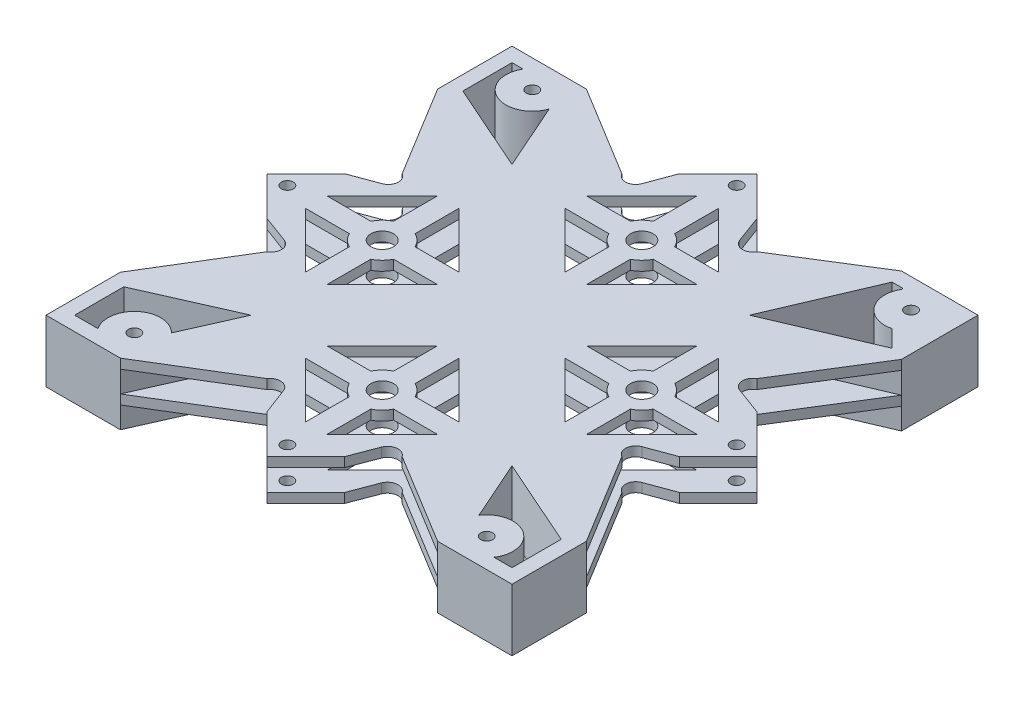
SolidWorks part; units mm, degrees
material "ABS"
ref_plane "Front Plane" through (0, 0, 0) normal (0, 0, 1) x (1, 0, 0)
ref_plane "Top Plane" through (0, 0, 0) normal (0, 1, 0) x (1, 0, 0)
ref_plane "Right Plane" through (0, 0, 0) normal (1, 0, 0) x (0, 0, -1)
sketch "Sketch1" plane through (0, 0, 0) normal (0, 1, 0) x (1, 0, 0)
  line L1 (0, 0) -> (97.6, 0)
  line L2 (0, 0) -> (0, 97.6)
  line L3 (0, 97.6) -> (97.6, 97.6)
  line L4 (97.6, 0) -> (97.6, 97.6)
  dimension "D1" = 97.6
  dimension "D2" = 97.6
extrude "Boss-Extrude1" add sketch "Sketch1" along normal blind 2
sketch "Sketch2" plane through (0, 0, 0) normal (0, -1, 0) x (-1, 0, 0)
  line L0 (-97.6, 97.6) -> (0, 0) construction
  line L1 (-97.6, 0) -> (0, 97.6) construction
  line L2 (-48.8, 97.6) -> (-48.8, 0) construction
  line L3 (-97.6, 97.6) -> (0, 97.6) construction
  line L4 (0, 0) -> (-97.6, 0) construction
  line L5 (-97.6, 48.8) -> (0, 48.8) construction
  line L6 (-97.6, 0) -> (-97.6, 97.6) construction
  line L7 (0, 97.6) -> (0, 0) construction
sketch "Sketch3" plane through (0, 0, 0) normal (0, -1, 0) x (1, 0, 0)
  line L0 (97.6, -97.6) -> (0, -97.6) construction
  line L1 (97.6, 0) -> (97.6, -97.6) construction
  line L2 (0, -97.6) -> (0, 0) construction
  line L3 (0, 0) -> (97.6, 0) construction
  line L4 (97.6, -94.6) -> (0, -94.6) construction
  line L5 (3, -97.6) -> (3, 0) construction
  line L6 (3, -94.6) -> (5.3161, -94.6)
  line L7 (3, -94.6) -> (3, -84.3)
  line L8 (3, -84.3) -> (21.4728, -76.1272)
  line L9 (97.6, 0) -> (0, -97.6) construction
  line L10 (21.4728, -76.1272) -> (13.3, -94.6)
  line L11 (21.4728, -21.4728) -> (13.3, -3)
  line L12 (3, -3) -> (13.3, -3)
  line L13 (0, -3) -> (97.6, -3) construction
  line L14 (3, -13.3) -> (3, -3)
  line L15 (3, -3) -> (7.8732, -3)
  line L16 (3, -13.3) -> (21.4728, -21.4728)
  line L17 (97.6, -97.6) -> (0, 0) construction
  line L18 (0, -97.6) -> (0, 0) construction
  line L19 (16.1614, -10.109) -> (21.4728, -21.4728) construction
  line L20 (94.6, -97.6) -> (94.6, 0) construction
  line L21 (94.6, -3) -> (94.6, -13.3)
  line L22 (94.6, -3) -> (84.3, -3)
  line L23 (94.6, -13.3) -> (76.1272, -21.4728)
  line L24 (76.1272, -21.4728) -> (84.3, -3)
  line L25 (94.6, -82.6) -> (73.6741, -73.6741)
  line L26 (73.6741, -73.6741) -> (82.6, -94.6)
  line L27 (94.6, -82.6) -> (82.6, -94.6) construction
  line L28 (94.6, -82.6) -> (91.0273, -86.1727)
  line L29 (82.6, -94.6) -> (85.1169, -94.6)
  line L30 (3, -94.6) -> (13.3, -94.6) construction
  circle A0 centre (89.66, -91.5) radius 1.25
  circle A1 centre (10.05, -91.8) radius 1.25
  circle A2 centre (12.45, -6.05) radius 1.25
  circle A3 centre (86.25, -6.05) radius 1.25
  circle A4 centre (89.66, -91.5) radius 5.5
  circle A5 centre (10.05, -91.8) radius 5.5
  circle A6 centre (12.45, -6.05) radius 5.5
  circle A7 centre (86.25, -6.05) radius 5.5
  dimension "D1" = 6.1
  dimension "D9" = 3
  dimension "D16" = 3
  dimension "D20" = 2.5
  dimension "D21" = 11
  dimension "D23" = 11
  dimension "D24" = 2.5
  dimension "D26" = 11
  dimension "D27" = 11
  dimension "D2" = 7.94
  dimension "D3" = 5.8
  dimension "D4" = 10.05
  dimension "D5" = 6.05
  dimension "D6" = 12.45
  dimension "D7" = 6.05
  dimension "D8" = 11.35
  dimension "D10" = 3
  dimension "D11" = 10.3
  dimension "D12" = 20.2
  dimension "D13" = 3
  dimension "D14" = 10.3
  dimension "D15" = 20.2
  dimension "D17" = 10.3
  dimension "D18" = 22.75
  dimension "D19" = 15
  dimension "D22" = 10.3
  dimension "D25" = 20.2
extrude "Cut-Extrude1" cut sketch "Sketch3" against normal blind 10
fillet "Fillet1" radius 0.2 1 edges at (85.1169, 1, -94.6)
sketch "Sketch5" plane through (0, 0, 0) normal (0, -1, 0) x (1, 0, 0)
  line L0 (78.0601, -69.3344) -> (24.4532, -15.7275) construction
  line L1 (15.9101, -24.6358) -> (67.2589, -75.9846) construction
  line L2 (97.6, -97.6) -> (0, 0) construction
  line L3 (25.594, -80.7317) -> (80.9701, -25.3556) construction
  line L4 (71.5743, -17.3) -> (16.8047, -72.0696) construction
  line L5 (97.6, 0) -> (0, -97.6) construction
  line L6 (51.05, -89.7671) -> (51.05, -80.6171)
  line L7 (46.55, -89.7671) -> (46.55, -80.6171)
  line L8 (48.8, -97.6) -> (48.8, 0) construction
  line L9 (51.05, -89.7671) -> (62.5825, -78.2346)
  line L10 (62.5825, -78.2346) -> (53.4325, -78.2346)
  line L11 (44.1675, -78.2346) -> (35.0175, -78.2346)
  line L12 (35.0175, -78.2346) -> (46.55, -89.7671)
  line L13 (48.8, -78.2346) -> (36.0473, -78.2346) construction
  line L14 (48.8, -73.7346) -> (36.0473, -73.7346) construction
  line L15 (44.1675, -73.7346) -> (35.0175, -73.7346)
  line L16 (46.55, -71.3521) -> (46.55, -62.2021)
  line L17 (53.4325, -73.7346) -> (62.5825, -73.7346)
  line L18 (51.05, -71.3521) -> (51.05, -62.2021)
  line L19 (62.5825, -73.7346) -> (51.05, -62.2021)
  line L20 (46.55, -62.2021) -> (35.0175, -73.7346)
  line L21 (48.8, -48.8) -> (-2.5605, -100.1605) construction
  line L22 (48.8, -48.8) -> (97.6, 0) construction
  line L23 (97.6, -97.6) -> (0, 0) construction
  line L24 (73.7346, -48.8) -> (73.7346, -36.0473) construction
  line L25 (78.2346, -48.8) -> (78.2346, -36.0473) construction
  line L26 (62.2021, -46.55) -> (73.7346, -35.0175)
  line L27 (73.7346, -62.5825) -> (62.2021, -51.05)
  line L28 (71.3521, -51.05) -> (62.2021, -51.05)
  line L29 (73.7346, -53.4325) -> (73.7346, -62.5825)
  line L30 (71.3521, -46.55) -> (62.2021, -46.55)
  line L31 (73.7346, -44.1675) -> (73.7346, -35.0175)
  line L32 (78.2346, -35.0175) -> (89.7671, -46.55)
  line L33 (78.2346, -44.1675) -> (78.2346, -35.0175)
  line L34 (78.2346, -62.5825) -> (78.2346, -53.4325)
  line L35 (89.7671, -51.05) -> (78.2346, -62.5825)
  line L36 (89.7671, -46.55) -> (80.6171, -46.55)
  line L37 (89.7671, -51.05) -> (80.6171, -51.05)
  line L38 (48.8, -19.3654) -> (61.5527, -19.3654) construction
  line L39 (48.8, -23.8654) -> (61.5527, -23.8654) construction
  line L40 (23.8654, -48.8) -> (23.8654, -61.5527) construction
  line L41 (19.3654, -48.8) -> (19.3654, -61.5527) construction
  line L42 (46.55, -7.8329) -> (46.55, -16.9829)
  line L43 (51.05, -7.8329) -> (51.05, -16.9829)
  line L44 (46.55, -7.8329) -> (35.0175, -19.3654)
  line L45 (35.0175, -19.3654) -> (44.1675, -19.3654)
  line L46 (53.4325, -19.3654) -> (62.5825, -19.3654)
  line L47 (62.5825, -19.3654) -> (51.05, -7.8329)
  line L48 (53.4325, -23.8654) -> (62.5825, -23.8654)
  line L49 (51.05, -26.2479) -> (51.05, -35.3979)
  line L50 (44.1675, -23.8654) -> (35.0175, -23.8654)
  line L51 (46.55, -26.2479) -> (46.55, -35.3979)
  line L52 (35.0175, -23.8654) -> (46.55, -35.3979)
  line L53 (51.05, -35.3979) -> (62.5825, -23.8654)
  line L54 (35.3979, -51.05) -> (23.8654, -62.5825)
  line L55 (23.8654, -35.0175) -> (35.3979, -46.55)
  line L56 (26.2479, -46.55) -> (35.3979, -46.55)
  line L57 (23.8654, -44.1675) -> (23.8654, -35.0175)
  line L58 (26.2479, -51.05) -> (35.3979, -51.05)
  line L59 (23.8654, -53.4325) -> (23.8654, -62.5825)
  line L60 (19.3654, -62.5825) -> (7.8329, -51.05)
  line L61 (19.3654, -53.4325) -> (19.3654, -62.5825)
  line L62 (19.3654, -35.0175) -> (19.3654, -44.1675)
  line L63 (7.8329, -46.55) -> (19.3654, -35.0175)
  line L64 (7.8329, -51.05) -> (16.9829, -51.05)
  line L65 (7.8329, -46.55) -> (16.9829, -46.55)
  line L66 (49.9, -97.6) -> (47.7, -97.6)
  line L67 (97.6, -97.6) -> (0, -97.6) construction
  line L68 (97.6, -48.8) -> (97.6, -49.9)
  line L69 (97.6, 0) -> (97.6, -97.6) construction
  line L70 (97.6, -48.8) -> (97.6, -47.7)
  line L71 (0, -49.9) -> (0, -48.8)
  line L72 (0, -97.6) -> (0, 0) construction
  line L73 (0, -48.8) -> (0, -47.7)
  line L74 (48.8, 0) -> (49.9, 0)
  line L75 (0, 0) -> (97.6, 0) construction
  line L76 (48.8, 0) -> (47.7, 0)
  circle A0 centre (48.8, -75.9846) radius 2.375
  circle A1 centre (48.8, -75.9846) radius 5.15
  circle A2 centre (75.9846, -48.8) radius 5.15
  circle A3 centre (75.9846, -48.8) radius 2.375
  circle A4 centre (48.8, -21.6154) radius 2.375
  circle A5 centre (48.8, -21.6154) radius 5.15
  circle A6 centre (21.6154, -48.8) radius 5.15
  circle A7 centre (21.6154, -48.8) radius 2.375
  circle A8 centre (95.8446, -48.8) radius 1.2484
  circle A9 centre (1.75, -48.8) radius 1.25
  circle A10 centre (48.8, -1.75) radius 1.25
  circle A11 centre (48.8, -95.8546) radius 1.25
  ellipse E0 centre (48.8, -97.6) end of major axis (48.8, -94.6046) minor radius 1.1
  ellipse E1 centre (97.6, -48.8) end of major axis (94.5962, -48.7938) minor radius 1.1
  ellipse E2 centre (0, -48.8) end of major axis (3, -48.8) minor radius 1.1
  ellipse E3 centre (48.8, 0) end of major axis (48.8, -3) minor radius 1.1
  dimension "D5" = 9.15
  dimension "D7" = 4.75
  dimension "D8" = 10.3
  dimension "D17" = 2.5
  dimension "D18" = 2.4968
  dimension "D19" = 2.5
  dimension "D20" = 2.5
  dimension "D1" = 6.17
  dimension "D2" = 6.17
  dimension "D3" = 6.17
  dimension "D4" = 6.17
  dimension "D6" = 2.25
  dimension "D9" = 2.25
  dimension "D10" = 1.1
  dimension "D11" = 1.1
  dimension "D12" = 1.1
  dimension "D13" = 3
  dimension "D14" = 2.25
  dimension "D15" = 2.25
  dimension "D16" = 3
  dimension "D21" = 2.9954
extrude "Cut-Extrude2" cut sketch "Sketch5" against normal blind 10
sketch "Sketch6" plane through (0, 2, 0) normal (0, 1, 0) x (1, 0, 0)
  line L0 (0, 0) -> (97.6, 0) construction
  line L1 (97.6, 0) -> (97.6, 97.6) construction
  line L2 (0, 97.6) -> (0, 0) construction
  line L3 (97.6, 97.6) -> (0, 97.6) construction
  line L4 (0, 0) -> (97.6, 0)
  line L5 (97.6, 0) -> (97.6, 97.6)
  line L6 (0, 97.6) -> (0, 0)
  line L7 (97.6, 97.6) -> (0, 97.6)
  line L9 (-2.5912, -2.712) -> (102.2762, -2.712)
  line L10 (-2.5912, -2.712) -> (-2.5912, 101.3587)
  line L11 (-2.5912, 101.3587) -> (102.2762, 101.3587)
  line L12 (102.2762, -2.712) -> (102.2762, 101.3587)
sketch "Sketch8" plane through (0, 2, 0) normal (0, 1, 0) x (1, 0, 0)
  line L0 (48.8, -2.4946) -> (100.0946, 48.8)
  line L1 (48.8, -2.4946) -> (-2.4946, 48.8)
  line L2 (100.0946, 48.8) -> (48.8, 100.0946)
  line L3 (-2.4946, 48.8) -> (48.8, 100.0946)
  line L5 (97.6, 0) -> (97.6, 97.6) construction
  line L6 (0, 0) -> (97.6, 0) construction
  line L7 (0, 97.6) -> (0, 0) construction
  line L8 (97.6, 97.6) -> (0, 97.6) construction
  line L9 (97.6, 0) -> (97.6, 97.6)
  line L10 (0, 0) -> (97.6, 0)
  line L11 (0, 97.6) -> (0, 0)
  line L12 (97.6, 97.6) -> (0, 97.6)
  line L14 (15.5813, 97.6) -> (25.0051, 76.2996)
  line L15 (21.4728, 76.1272) -> (15.285, 90.1134) construction
  line L16 (21.3004, 72.5949) -> (0, 82.0187)
  line L18 (3, 84.3) -> (21.4728, 76.1272) construction
  circle A0 centre (95.8446, 48.8) radius 1.2484 construction
  dimension "D1" = 4.25
  dimension "D2" = 3.3
  dimension "D3" = 3.3
extrude "Boss-Extrude2" add sketch "Sketch6" against normal blind 2
sketch "Sketch9" plane through (0, 2, 0) normal (0, 1, 0) x (1, 0, 0)
  line L0 (97.6, 97.6) -> (0, 97.6) construction
  line L1 (15.5813, 97.6) -> (25.0051, 76.2996) construction
  line L2 (21.3004, 72.5949) -> (0, 82.0187) construction
  line L3 (-2.4946, 48.8) -> (48.8, 100.0946) construction
  line L4 (100.0946, 48.8) -> (48.8, 100.0946) construction
  line L5 (48.8, -2.4946) -> (100.0946, 48.8) construction
  line L6 (97.6, 0) -> (97.6, 97.6) construction
  line L7 (48.8, -2.4946) -> (-2.4946, 48.8) construction
  line L8 (0, 97.6) -> (0, 0) construction
  line L9 (0, 0) -> (97.6, 0) construction
  line L10 (97.6, 97.6) -> (0, 97.6)
  line L11 (15.5813, 97.6) -> (27.9447, 69.6553)
  line L12 (27.9447, 69.6553) -> (0, 82.0187)
  line L13 (-2.4946, 48.8) -> (48.8, 100.0946) construction
  line L14 (100.0946, 48.8) -> (48.8, 100.0946) construction
  line L15 (48.8, -2.4946) -> (100.0946, 48.8) construction
  line L16 (97.6, 0) -> (97.6, 97.6)
  line L17 (48.8, -2.4946) -> (-2.4946, 48.8) construction
  line L18 (0, 97.6) -> (0, 0)
  line L19 (0, 0) -> (97.6, 0)
  line L20 (97.6, 0) -> (0, 97.6) construction
  line L21 (48.8, 100.0946) -> (40.6683, 91.9628)
  line L22 (48.8, 100.0946) -> (56.9317, 91.9628)
  line L23 (-2.4946, 48.8) -> (5.6372, 56.9317)
  line L24 (-2.4946, 48.8) -> (5.6372, 40.6683)
  line L25 (48.8, -2.4946) -> (56.9317, 5.6372)
  line L26 (48.8, -2.4946) -> (40.6683, 5.6372)
  line L27 (100.0946, 48.8) -> (91.9628, 56.9317)
  line L28 (100.0946, 48.8) -> (91.9628, 40.6683)
  line L29 (0, 15.5813) -> (27.9447, 27.9447)
  line L30 (97.6, 97.6) -> (0, 0) construction
  line L31 (27.9447, 27.9447) -> (15.5813, 0)
  line L32 (3, 13.3) -> (21.4728, 21.4728) construction
  line L33 (21.4728, 21.4728) -> (16.3605, 9.9176) construction
  line L34 (69.6553, 27.9447) -> (82.0187, 0)
  line L35 (69.6553, 27.9447) -> (97.6, 15.5813)
  line L36 (76.1272, 21.4728) -> (81.6302, 9.0345) construction
  line L37 (94.6, 13.3) -> (76.1272, 21.4728) construction
  line L38 (53.3731, 44.2269) -> (46.5346, 51.0654) construction
  line L39 (69.6553, 69.6553) -> (97.6, 81.575)
  line L40 (81.575, 97.6) -> (69.6553, 69.6553)
  line L41 (5.6372, 56.9317) -> (11.3654, 59.05)
  line L42 (73.6741, 73.6741) -> (82.6, 94.6) construction
  line L43 (5.6372, 40.6683) -> (11.3654, 38.55)
  line L44 (94.6, 82.6) -> (73.6741, 73.6741) construction
  line L45 (62.9421, 85.9524) -> (81.575, 97.6)
  line L46 (97.6, 81.575) -> (85.9524, 62.9421)
  line L47 (0, 15.5813) -> (11.6476, 34.6579)
  line L48 (15.5813, 0) -> (34.6579, 11.6476)
  line L49 (0, 82.0187) -> (11.6476, 62.9421)
  line L50 (15.5813, 97.6) -> (34.6579, 85.9524)
  line L51 (97.6, 15.5813) -> (85.9524, 34.6579)
  line L52 (82.0187, 0) -> (62.9421, 11.6476)
  line L53 (40.6683, 91.9628) -> (38.55, 86.2346)
  line L54 (56.9317, 91.9628) -> (59.05, 86.2346)
  line L55 (48.8, 97.6) -> (48.8, 0) construction
  line L56 (36.745, 88.0396) -> (40.7838, 84.0008) construction
  line L57 (35.0175, 78.2346) -> (46.55, 89.7671) construction
  line L58 (56.8162, 13.5992) -> (59.4365, 10.7785) construction
  line L59 (62.5825, 19.3654) -> (51.05, 7.8329) construction
  line L60 (56.9317, 5.6372) -> (59.05, 11.1946)
  line L61 (40.6683, 5.6372) -> (38.55, 11.1946)
  line L62 (91.9628, 56.9317) -> (86.2346, 59.05)
  line L63 (91.9628, 40.6683) -> (86.2346, 38.55)
  line L64 (84.0008, 40.7838) -> (88.4683, 36.3162) construction
  line L65 (78.2346, 35.0175) -> (89.7671, 46.55) construction
  line L66 (97.6, 48.8) -> (0, 48.8) construction
  line L67 (13.5992, 40.7838) -> (7.9744, 35.1589) construction
  line L68 (7.8329, 46.55) -> (19.3654, 35.0175) construction
  line L70 (-2.5912, 101.3587) -> (102.2762, 101.3587)
  line L71 (-2.5912, 101.3587) -> (-2.5912, -2.712)
  line L72 (-2.5912, -2.712) -> (102.2762, -2.712)
  line L73 (102.2762, 101.3587) -> (102.2762, -2.712)
  arc A0 (38.55, 86.2346) -> (34.6579, 85.9524) centre (36.5398, 86.9779) cw
  arc A1 (59.05, 86.2346) -> (62.9421, 85.9524) centre (61.0602, 86.9779) ccw
  arc A2 (38.55, 11.1946) -> (34.6579, 11.6476) centre (36.486, 10.4079) ccw
  arc A3 (59.05, 11.1946) -> (62.9421, 11.6476) centre (61.114, 10.4079) cw
  arc A4 (86.2346, 59.05) -> (85.9524, 62.9421) centre (86.9779, 61.0602) cw
  arc A5 (86.2346, 38.55) -> (85.9524, 34.6579) centre (86.9779, 36.5398) ccw
  arc A6 (11.3654, 38.55) -> (11.6476, 34.6579) centre (10.6221, 36.5398) cw
  arc A7 (11.3654, 59.05) -> (11.6476, 62.9421) centre (10.6221, 61.0602) ccw
  point P48 (62.9421, 85.9524)
  dimension "D1" = 11.5
  dimension "D2" = 3.3
  dimension "D3" = 3.3
  dimension "D4" = 20
  dimension "D5" = 20
  dimension "D6" = 20
  dimension "D7" = 20
  dimension "D8" = 20
  dimension "D9" = 20
  dimension "D10" = 20
  dimension "D11" = 20
  dimension "D12" = 10.25
  dimension "D13" = 10.25
  dimension "D14" = 10.25
  dimension "D15" = 10.25
  dimension "D16" = 10.25
  dimension "D17" = 10.25
  dimension "D18" = 10.25
  dimension "D19" = 10.25
extrude "Cut-Extrude3" cut sketch "Sketch9" against normal blind 2 contours L73 L70 L71 L72 L27 L28 L16 L19 L25 L26 L18 L24 L23 L10 L21 L22 | A0 L53 L21 L10 L50 | L54 A1 L45 L10 L22 | A4 L62 L27 L16 L46 | L63 A5 L51 L16 L28 | A3 L60 L25 L19 L52 | L61 A2 L48 L19 L26 | A6 L43 L24 L18 L47 | L41 A7 L49 L18 L23
sketch "Sketch11" plane through (0, 0, 0) normal (0, -1, 0) x (1, 0, 0)
  line L0 (69.6553, -27.9447) -> (82.0187, 0) construction
  line L1 (69.6553, -27.9447) -> (82.0187, 0)
  line L2 (69.6553, -27.9447) -> (97.6, -15.5813) construction
  line L3 (73.6741, -73.6741) -> (82.6, -94.6) construction
  line L4 (94.6, -82.6) -> (73.6741, -73.6741) construction
  line L6 (94.6, -82.6) -> (91.0273, -86.1727) construction
  line L7 (94.6, -3) -> (94.6, -13.3) construction
  line L8 (94.6, -13.3) -> (76.1272, -21.4728) construction
  line L9 (94.6, -3) -> (90.8268, -3) construction
  line L10 (76.1272, -21.4728) -> (81.6302, -9.0345) construction
  line L11 (81.575, -97.6) -> (69.6553, -69.6553) construction
  line L12 (69.6553, -69.6553) -> (97.6, -81.575) construction
  line L13 (15.5813, -97.6) -> (0, -97.6) construction
  line L14 (0, -97.6) -> (0, -82.0187) construction
  line L15 (3, -84.3) -> (21.4728, -76.1272) construction
  line L16 (3, -94.6) -> (3, -84.3) construction
  line L17 (27.9447, -69.6553) -> (0, -82.0187) construction
  line L18 (15.5813, -97.6) -> (27.9447, -69.6553) construction
  line L19 (21.4728, -76.1272) -> (15.285, -90.1134) construction
  line L20 (3, -94.6) -> (5.3161, -94.6) construction
  line L21 (97.6, -81.575) -> (97.6, -97.6) construction
  line L22 (97.6, -97.6) -> (81.575, -97.6) construction
  line L23 (97.6, 0) -> (97.6, -15.5813) construction
  line L24 (82.0187, 0) -> (97.6, 0) construction
  line L25 (27.9447, -27.9447) -> (15.5813, 0) construction
  line L26 (0, -15.5813) -> (27.9447, -27.9447) construction
  line L27 (3, -13.3) -> (21.4728, -21.4728) construction
  line L28 (21.4728, -21.4728) -> (16.3605, -9.9176) construction
  line L29 (3, -3) -> (7.8732, -3) construction
  line L30 (3, -13.3) -> (3, -3) construction
  line L31 (0, 0) -> (0, -15.5813) construction
  line L32 (0, 0) -> (15.5813, 0) construction
  line L33 (69.6553, -27.9447) -> (97.6, -15.5813)
  line L34 (73.6741, -73.6741) -> (82.6, -94.6)
  line L35 (94.6, -82.6) -> (73.6741, -73.6741)
  line L36 (82.6, -94.6) -> (84.7529, -94.6) construction
  line L37 (94.6, -82.6) -> (91.0273, -86.1727)
  line L38 (94.6, -3) -> (94.6, -13.3)
  line L39 (94.6, -13.3) -> (76.1272, -21.4728)
  line L40 (94.6, -3) -> (90.8268, -3)
  line L41 (76.1272, -21.4728) -> (81.6302, -9.0345)
  line L42 (81.575, -97.6) -> (69.6553, -69.6553)
  line L43 (69.6553, -69.6553) -> (97.6, -81.575)
  line L44 (15.5813, -97.6) -> (0, -97.6)
  line L45 (0, -97.6) -> (0, -82.0187)
  line L46 (3, -84.3) -> (21.4728, -76.1272)
  line L47 (3, -94.6) -> (3, -84.3)
  line L48 (27.9447, -69.6553) -> (0, -82.0187)
  line L49 (15.5813, -97.6) -> (27.9447, -69.6553)
  line L50 (21.4728, -76.1272) -> (15.285, -90.1134)
  line L51 (3, -94.6) -> (5.3161, -94.6)
  line L52 (97.6, -81.575) -> (97.6, -97.6)
  line L53 (97.6, -97.6) -> (81.575, -97.6)
  line L54 (97.6, 0) -> (97.6, -15.5813)
  line L55 (82.0187, 0) -> (97.6, 0)
  line L56 (27.9447, -27.9447) -> (15.5813, 0)
  line L57 (0, -15.5813) -> (27.9447, -27.9447)
  line L58 (3, -13.3) -> (21.4728, -21.4728)
  line L59 (21.4728, -21.4728) -> (16.3605, -9.9176)
  line L60 (3, -3) -> (7.8732, -3)
  line L61 (3, -13.3) -> (3, -3)
  line L62 (0, 0) -> (0, -15.5813)
  line L63 (0, 0) -> (15.5813, 0)
  line L64 (26.1692, -27.1592) -> (70.3917, -71.3816)
  line L65 (71.3816, -70.3917) -> (27.1592, -26.1692)
  line L66 (97.6, -97.6) -> (0, 0) construction
  line L67 (26.1692, -70.4408) -> (70.4408, -26.1692)
  line L68 (27.1592, -71.4308) -> (71.4308, -27.1592)
  line L69 (97.6, 0) -> (0, -97.6) construction
  line L70 (82.6, -94.6) -> (84.7529, -94.6)
  arc A0 (81.6302, -9.0345) -> (90.8268, -3) centre (86.25, -6.05) ccw construction
  arc A1 (81.6302, -9.0345) -> (90.8268, -3) centre (86.25, -6.05) ccw
  arc A3 (15.285, -90.1134) -> (5.3161, -94.6) centre (10.05, -91.8) ccw construction
  circle A4 centre (10.05, -91.8) radius 1.25 construction
  circle A5 centre (86.25, -6.05) radius 1.25 construction
  arc A6 (7.8732, -3) -> (16.3605, -9.9176) centre (12.45, -6.05) ccw construction
  circle A7 centre (12.45, -6.05) radius 1.25 construction
  arc A8 (91.0273, -86.1727) -> (84.925, -94.2982) centre (89.66, -91.5) ccw construction
  arc A9 (15.285, -90.1134) -> (5.3161, -94.6) centre (10.05, -91.8) ccw
  circle A10 centre (10.05, -91.8) radius 1.25
  circle A11 centre (86.25, -6.05) radius 1.25
  arc A12 (7.8732, -3) -> (16.3605, -9.9176) centre (12.45, -6.05) ccw
  circle A13 centre (12.45, -6.05) radius 1.25
  circle A14 centre (89.66, -91.5) radius 1.25 construction
  circle A15 centre (89.66, -91.5) radius 1.25
  arc A16 (84.7529, -94.6) -> (84.925, -94.2982) centre (84.7529, -94.4) ccw construction
  arc A17 (91.0273, -86.1727) -> (84.925, -94.2982) centre (89.66, -91.5) ccw
  arc A18 (84.7529, -94.6) -> (84.925, -94.2982) centre (84.7529, -94.4) ccw
  dimension "D1" = 0.7
  dimension "D2" = 0.7
  dimension "D3" = 0.7
  dimension "D4" = 0.7
extrude "Boss-Extrude3" add sketch "Sketch11" along normal blind 4.5 contours L53 L52 L43 L42 A18 L70 L34 L35 L37 A17 A15 | L49 L68 L64 L67 L48 | L65 L68 L33 L1 L67 | L64 L67 L65 L56 L57 | L68 L64 L42 L43 L65 | L64 L68 L65 L67 | L44 L49 L48 L45 A10 L50 A9 L51 L47 L46 | L63 L62 L57 L56 A13 L60 A12 L59 L58 L61 | L55 L1 L33 L54 A11 L41 A1 L40 L38 L39
sketch "Sketch12" plane through (0, -4.5, 0) normal (0, -1, 0) x (1, 0, 0)
  line L0 (26.8763, -71.1479) -> (71.1483, -26.876)
  line L1 (26.8763, -71.1479) -> (26.4521, -70.7237)
  line L2 (26.4521, -26.8763) -> (70.724, -71.1483)
  line L3 (71.1483, -26.876) -> (70.724, -26.4517)
  line L4 (26.4521, -70.7237) -> (70.724, -26.4517)
  line L5 (26.4521, -26.8763) -> (26.8763, -26.4521)
  line L6 (70.724, -71.1483) -> (71.1483, -70.724)
  line L7 (26.8763, -26.4521) -> (71.1483, -70.724)
  line L8 (48.8, -49.7899) -> (70.3917, -71.3816) construction
  line L9 (48.8, -47.8101) -> (70.4408, -26.1692) construction
  line L10 (49.7899, -48.8) -> (71.4308, -27.1592) construction
  line L11 (71.3816, -70.3917) -> (49.7899, -48.8) construction
  line L12 (26.1692, -70.4408) -> (27.1592, -71.4308) construction
  line L13 (26.1692, -27.1592) -> (27.1592, -26.1692) construction
  dimension "D1" = 0.6
  dimension "D2" = 0.4
  dimension "D3" = 0.6
  dimension "D4" = 0.4
  dimension "D5" = 62.61
  dimension "D6" = 62.61
extrude "Cut-Extrude4" cut sketch "Sketch12" against normal blind 4.5 contours L4 L1 L0 L2 | L4 L7 L0 L3
sketch "Sketch13" plane through (0, -4.5, 0) normal (0, -1, 0) x (1, 0, 0)
  line L0 (0, -97.6) -> (0, -82.0187) construction
  line L1 (15.5813, -97.6) -> (0, -97.6) construction
  line L2 (34.6579, -85.9524) -> (15.5813, -97.6) construction
  line L3 (38.55, -86.2346) -> (40.6683, -91.9628) construction
  line L4 (40.6683, -91.9628) -> (48.8, -100.0946) construction
  line L5 (56.9317, -91.9628) -> (48.8, -100.0946) construction
  line L6 (59.05, -86.2346) -> (56.9317, -91.9628) construction
  line L7 (81.575, -97.6) -> (62.9421, -85.9524) construction
  line L8 (97.6, -97.6) -> (81.575, -97.6) construction
  line L9 (97.6, -81.575) -> (97.6, -97.6) construction
  line L10 (85.9524, -62.9421) -> (97.6, -81.575) construction
  line L11 (86.2346, -59.05) -> (91.9628, -56.9317) construction
  line L12 (91.9628, -56.9317) -> (100.0946, -48.8) construction
  line L13 (91.9628, -40.6683) -> (100.0946, -48.8) construction
  line L14 (86.2346, -38.55) -> (91.9628, -40.6683) construction
  line L15 (85.9524, -34.6579) -> (97.6, -15.5813) construction
  line L16 (97.6, 0) -> (97.6, -15.5813) construction
  line L17 (82.0187, 0) -> (97.6, 0) construction
  line L18 (70.4408, -26.1692) -> (82.0187, 0) construction
  line L19 (70.4408, -26.1692) -> (82.0187, 0) construction
  line L20 (62.9421, -11.6476) -> (82.0187, 0) construction
  line L21 (59.05, -11.1946) -> (56.9317, -5.6372) construction
  line L22 (56.9317, -5.6372) -> (48.8, 2.4946) construction
  line L23 (40.6683, -5.6372) -> (48.8, 2.4946) construction
  line L24 (38.55, -11.1946) -> (40.6683, -5.6372) construction
  line L25 (34.6579, -11.6476) -> (15.5813, 0) construction
  line L26 (0, 0) -> (15.5813, 0) construction
  line L27 (0, 0) -> (0, -15.5813) construction
  line L28 (11.6476, -34.6579) -> (0, -15.5813) construction
  line L29 (11.3654, -38.55) -> (5.6372, -40.6683) construction
  line L30 (5.6372, -40.6683) -> (-2.4946, -48.8) construction
  line L31 (5.6372, -56.9317) -> (-2.4946, -48.8) construction
  line L32 (11.3654, -59.05) -> (5.6372, -56.9317) construction
  line L33 (11.6476, -62.9421) -> (0, -82.0187) construction
  line L34 (0, -97.6) -> (0, -82.0187)
  line L35 (15.5813, -97.6) -> (0, -97.6)
  line L36 (34.6579, -85.9524) -> (15.5813, -97.6)
  line L37 (38.55, -86.2346) -> (40.6683, -91.9628)
  line L38 (40.6683, -91.9628) -> (48.8, -100.0946)
  line L39 (56.9317, -91.9628) -> (48.8, -100.0946)
  line L40 (59.05, -86.2346) -> (56.9317, -91.9628)
  line L41 (81.575, -97.6) -> (62.9421, -85.9524)
  line L42 (97.6, -97.6) -> (81.575, -97.6)
  line L43 (97.6, -81.575) -> (97.6, -97.6)
  line L44 (85.9524, -62.9421) -> (97.6, -81.575)
  line L45 (86.2346, -59.05) -> (91.9628, -56.9317)
  line L46 (91.9628, -56.9317) -> (100.0946, -48.8)
  line L47 (91.9628, -40.6683) -> (100.0946, -48.8)
  line L48 (86.2346, -38.55) -> (91.9628, -40.6683)
  line L49 (85.9524, -34.6579) -> (97.6, -15.5813)
  line L50 (97.6, 0) -> (97.6, -15.5813)
  line L51 (82.0187, 0) -> (97.6, 0)
  line L52 (70.4408, -26.1692) -> (82.0187, 0)
  line L53 (70.4408, -26.1692) -> (82.0187, 0)
  line L54 (62.9421, -11.6476) -> (82.0187, 0)
  line L55 (59.05, -11.1946) -> (56.9317, -5.6372)
  line L56 (56.9317, -5.6372) -> (48.8, 2.4946)
  line L57 (40.6683, -5.6372) -> (48.8, 2.4946)
  line L58 (38.55, -11.1946) -> (40.6683, -5.6372)
  line L59 (34.6579, -11.6476) -> (15.5813, 0)
  line L60 (0, 0) -> (15.5813, 0)
  line L61 (0, 0) -> (0, -15.5813)
  line L62 (11.6476, -34.6579) -> (0, -15.5813)
  line L63 (11.3654, -38.55) -> (5.6372, -40.6683)
  line L64 (5.6372, -40.6683) -> (-2.4946, -48.8)
  line L65 (5.6372, -56.9317) -> (-2.4946, -48.8)
  line L66 (11.3654, -59.05) -> (5.6372, -56.9317)
  line L67 (11.6476, -62.9421) -> (0, -82.0187)
  arc A0 (38.55, -86.2346) -> (34.6579, -85.9524) centre (36.5398, -86.9779) ccw construction
  arc A1 (62.9421, -85.9524) -> (59.05, -86.2346) centre (61.0602, -86.9779) ccw construction
  arc A2 (86.2346, -59.05) -> (85.9524, -62.9421) centre (86.9779, -61.0602) ccw construction
  arc A3 (85.9524, -34.6579) -> (86.2346, -38.55) centre (86.9779, -36.5398) ccw construction
  arc A4 (59.05, -11.1946) -> (62.9421, -11.6476) centre (61.114, -10.4079) ccw construction
  arc A5 (34.6579, -11.6476) -> (38.55, -11.1946) centre (36.486, -10.4079) ccw construction
  arc A6 (11.3654, -38.55) -> (11.6476, -34.6579) centre (10.6221, -36.5398) ccw construction
  arc A7 (11.6476, -62.9421) -> (11.3654, -59.05) centre (10.6221, -61.0602) ccw construction
  arc A8 (38.55, -86.2346) -> (34.6579, -85.9524) centre (36.5398, -86.9779) ccw
  arc A9 (62.9421, -85.9524) -> (59.05, -86.2346) centre (61.0602, -86.9779) ccw
  arc A10 (86.2346, -59.05) -> (85.9524, -62.9421) centre (86.9779, -61.0602) ccw
  arc A11 (85.9524, -34.6579) -> (86.2346, -38.55) centre (86.9779, -36.5398) ccw
  arc A12 (59.05, -11.1946) -> (62.9421, -11.6476) centre (61.114, -10.4079) ccw
  arc A13 (34.6579, -11.6476) -> (38.55, -11.1946) centre (36.486, -10.4079) ccw
  arc A14 (11.3654, -38.55) -> (11.6476, -34.6579) centre (10.6221, -36.5398) ccw
  arc A15 (11.6476, -62.9421) -> (11.3654, -59.05) centre (10.6221, -61.0602) ccw
extrude "Boss-Extrude4" add sketch "Sketch13" along normal blind 2
sketch "Sketch15" plane through (0, -6.5, 0) normal (0, -1, 0) x (1, 0, 0)
  line L0 (3, -13.3) -> (3, -3) construction
  line L1 (3, -3) -> (7.8732, -3) construction
  line L2 (3, -13.3) -> (21.4728, -21.4728) construction
  line L3 (21.4728, -21.4728) -> (16.3605, -9.9176) construction
  line L4 (46.55, -7.8329) -> (35.0175, -19.3654) construction
  line L5 (46.55, -7.8329) -> (46.55, -16.9829) construction
  line L6 (51.05, -7.8329) -> (51.05, -16.9829) construction
  line L7 (35.0175, -19.3654) -> (44.1675, -19.3654) construction
  line L8 (44.1675, -23.8654) -> (35.0175, -23.8654) construction
  line L9 (35.0175, -23.8654) -> (46.55, -35.3979) construction
  line L10 (53.4325, -19.3654) -> (62.5825, -19.3654) construction
  line L11 (62.5825, -19.3654) -> (51.05, -7.8329) construction
  line L12 (53.4325, -23.8654) -> (62.5825, -23.8654) construction
  line L13 (51.05, -26.2479) -> (51.05, -35.3979) construction
  line L14 (51.05, -35.3979) -> (62.5825, -23.8654) construction
  line L15 (94.6, -3) -> (94.6, -13.3) construction
  line L16 (94.6, -3) -> (90.8268, -3) construction
  line L17 (94.6, -13.3) -> (76.1272, -21.4728) construction
  line L18 (76.1272, -21.4728) -> (81.6302, -9.0345) construction
  line L19 (7.8329, -46.55) -> (19.3654, -35.0175) construction
  line L20 (7.8329, -46.55) -> (16.9829, -46.55) construction
  line L21 (19.3654, -35.0175) -> (19.3654, -44.1675) construction
  line L22 (23.8654, -44.1675) -> (23.8654, -35.0175) construction
  line L23 (23.8654, -35.0175) -> (35.3979, -46.55) construction
  line L24 (26.2479, -46.55) -> (35.3979, -46.55) construction
  line L25 (26.2479, -51.05) -> (35.3979, -51.05) construction
  line L26 (23.8654, -53.4325) -> (23.8654, -62.5825) construction
  line L27 (35.3979, -51.05) -> (23.8654, -62.5825) construction
  line L28 (19.3654, -53.4325) -> (19.3654, -62.5825) construction
  line L29 (7.8329, -51.05) -> (16.9829, -51.05) construction
  line L30 (19.3654, -62.5825) -> (7.8329, -51.05) construction
  line L31 (21.4728, -76.1272) -> (15.285, -90.1134) construction
  line L32 (3, -84.3) -> (21.4728, -76.1272) construction
  line L33 (3, -94.6) -> (5.3161, -94.6) construction
  line L34 (3, -94.6) -> (3, -84.3) construction
  line L35 (62.5825, -73.7346) -> (51.05, -62.2021) construction
  line L36 (53.4325, -73.7346) -> (62.5825, -73.7346) construction
  line L37 (51.05, -71.3521) -> (51.05, -62.2021) construction
  line L38 (46.55, -71.3521) -> (46.55, -62.2021) construction
  line L39 (44.1675, -73.7346) -> (35.0175, -73.7346) construction
  line L40 (46.55, -62.2021) -> (35.0175, -73.7346) construction
  line L41 (35.0175, -78.2346) -> (46.55, -89.7671) construction
  line L42 (44.1675, -78.2346) -> (35.0175, -78.2346) construction
  line L43 (46.55, -89.7671) -> (46.55, -80.6171) construction
  line L44 (51.05, -89.7671) -> (51.05, -80.6171) construction
  line L45 (62.5825, -78.2346) -> (53.4325, -78.2346) construction
  line L46 (51.05, -89.7671) -> (62.5825, -78.2346) construction
  line L47 (94.6, -82.6) -> (73.6741, -73.6741) construction
  line L48 (73.6741, -73.6741) -> (82.6, -94.6) construction
  line L49 (82.6, -94.6) -> (84.7529, -94.6) construction
  line L50 (94.6, -82.6) -> (91.0273, -86.1727) construction
  line L51 (78.2346, -35.0175) -> (89.7671, -46.55) construction
  line L52 (89.7671, -46.55) -> (80.6171, -46.55) construction
  line L53 (78.2346, -44.1675) -> (78.2346, -35.0175) construction
  line L54 (89.7671, -51.05) -> (80.6171, -51.05) construction
  line L55 (78.2346, -62.5825) -> (78.2346, -53.4325) construction
  line L56 (89.7671, -51.05) -> (78.2346, -62.5825) construction
  line L57 (73.7346, -44.1675) -> (73.7346, -35.0175) construction
  line L58 (62.2021, -46.55) -> (73.7346, -35.0175) construction
  line L59 (71.3521, -46.55) -> (62.2021, -46.55) construction
  line L60 (71.3521, -51.05) -> (62.2021, -51.05) construction
  line L61 (73.7346, -62.5825) -> (62.2021, -51.05) construction
  line L62 (73.7346, -53.4325) -> (73.7346, -62.5825) construction
  line L63 (3, -13.3) -> (3, -3)
  line L64 (3, -3) -> (7.8732, -3)
  line L65 (3, -13.3) -> (21.4728, -21.4728)
  line L66 (21.4728, -21.4728) -> (16.3605, -9.9176)
  line L67 (46.55, -7.8329) -> (35.0175, -19.3654)
  line L68 (46.55, -7.8329) -> (46.55, -16.9829)
  line L69 (51.05, -7.8329) -> (51.05, -16.9829)
  line L70 (35.0175, -19.3654) -> (44.1675, -19.3654)
  line L71 (44.1675, -23.8654) -> (35.0175, -23.8654)
  line L72 (35.0175, -23.8654) -> (46.55, -35.3979)
  line L73 (53.4325, -19.3654) -> (62.5825, -19.3654)
  line L74 (62.5825, -19.3654) -> (51.05, -7.8329)
  line L75 (53.4325, -23.8654) -> (62.5825, -23.8654)
  line L76 (51.05, -26.2479) -> (51.05, -35.3979)
  line L77 (51.05, -35.3979) -> (62.5825, -23.8654)
  line L78 (94.6, -3) -> (94.6, -13.3)
  line L79 (94.6, -3) -> (90.8268, -3)
  line L80 (94.6, -13.3) -> (76.1272, -21.4728)
  line L81 (76.1272, -21.4728) -> (81.6302, -9.0345)
  line L82 (7.8329, -46.55) -> (19.3654, -35.0175)
  line L83 (7.8329, -46.55) -> (16.9829, -46.55)
  line L84 (19.3654, -35.0175) -> (19.3654, -44.1675)
  line L85 (23.8654, -44.1675) -> (23.8654, -35.0175)
  line L86 (23.8654, -35.0175) -> (35.3979, -46.55)
  line L87 (26.2479, -46.55) -> (35.3979, -46.55)
  line L88 (26.2479, -51.05) -> (35.3979, -51.05)
  line L89 (23.8654, -53.4325) -> (23.8654, -62.5825)
  line L90 (35.3979, -51.05) -> (23.8654, -62.5825)
  line L91 (19.3654, -53.4325) -> (19.3654, -62.5825)
  line L92 (7.8329, -51.05) -> (16.9829, -51.05)
  line L93 (19.3654, -62.5825) -> (7.8329, -51.05)
  line L94 (21.4728, -76.1272) -> (15.285, -90.1134)
  line L95 (3, -84.3) -> (21.4728, -76.1272)
  line L96 (3, -94.6) -> (5.3161, -94.6)
  line L97 (3, -94.6) -> (3, -84.3)
  line L98 (62.5825, -73.7346) -> (51.05, -62.2021)
  line L99 (53.4325, -73.7346) -> (62.5825, -73.7346)
  line L100 (51.05, -71.3521) -> (51.05, -62.2021)
  line L101 (46.55, -71.3521) -> (46.55, -62.2021)
  line L102 (44.1675, -73.7346) -> (35.0175, -73.7346)
  line L103 (46.55, -62.2021) -> (35.0175, -73.7346)
  line L104 (35.0175, -78.2346) -> (46.55, -89.7671)
  line L105 (44.1675, -78.2346) -> (35.0175, -78.2346)
  line L106 (46.55, -89.7671) -> (46.55, -80.6171)
  line L107 (51.05, -89.7671) -> (51.05, -80.6171)
  line L108 (62.5825, -78.2346) -> (53.4325, -78.2346)
  line L109 (51.05, -89.7671) -> (62.5825, -78.2346)
  line L110 (94.6, -82.6) -> (73.6741, -73.6741)
  line L111 (73.6741, -73.6741) -> (82.6, -94.6)
  line L112 (82.6, -94.6) -> (84.7529, -94.6)
  line L113 (94.6, -82.6) -> (91.0273, -86.1727)
  line L114 (78.2346, -35.0175) -> (89.7671, -46.55)
  line L115 (89.7671, -46.55) -> (80.6171, -46.55)
  line L116 (78.2346, -44.1675) -> (78.2346, -35.0175)
  line L117 (89.7671, -51.05) -> (80.6171, -51.05)
  line L118 (78.2346, -62.5825) -> (78.2346, -53.4325)
  line L119 (89.7671, -51.05) -> (78.2346, -62.5825)
  line L120 (73.7346, -44.1675) -> (73.7346, -35.0175)
  line L121 (62.2021, -46.55) -> (73.7346, -35.0175)
  line L122 (71.3521, -46.55) -> (62.2021, -46.55)
  line L123 (71.3521, -51.05) -> (62.2021, -51.05)
  line L124 (73.7346, -62.5825) -> (62.2021, -51.05)
  line L125 (73.7346, -53.4325) -> (73.7346, -62.5825)
  line L126 (46.55, -26.2479) -> (46.55, -35.3979) construction
  line L127 (46.55, -26.2479) -> (46.55, -35.3979)
  circle A0 centre (12.45, -6.05) radius 1.25 construction
  arc A1 (7.8732, -3) -> (16.3605, -9.9176) centre (12.45, -6.05) ccw construction
  circle A2 centre (48.8, -1.75) radius 1.25 construction
  arc A3 (46.55, -16.9829) -> (44.1675, -19.3654) centre (48.8, -21.6154) ccw construction
  arc A4 (44.1675, -23.8654) -> (46.55, -26.2479) centre (48.8, -21.6154) ccw construction
  circle A5 centre (48.8, -21.6154) radius 2.375 construction
  arc A6 (53.4325, -19.3654) -> (51.05, -16.9829) centre (48.8, -21.6154) ccw construction
  arc A7 (51.05, -26.2479) -> (53.4325, -23.8654) centre (48.8, -21.6154) ccw construction
  circle A8 centre (86.25, -6.05) radius 1.25 construction
  arc A9 (81.6302, -9.0345) -> (90.8268, -3) centre (86.25, -6.05) ccw construction
  arc A10 (19.3654, -44.1675) -> (16.9829, -46.55) centre (21.6154, -48.8) ccw construction
  circle A11 centre (21.6154, -48.8) radius 2.375 construction
  arc A12 (26.2479, -46.55) -> (23.8654, -44.1675) centre (21.6154, -48.8) ccw construction
  arc A13 (23.8654, -53.4325) -> (26.2479, -51.05) centre (21.6154, -48.8) ccw construction
  arc A14 (16.9829, -51.05) -> (19.3654, -53.4325) centre (21.6154, -48.8) ccw construction
  circle A15 centre (10.05, -91.8) radius 1.25 construction
  arc A16 (15.285, -90.1134) -> (5.3161, -94.6) centre (10.05, -91.8) ccw construction
  arc A17 (53.4325, -73.7346) -> (51.05, -71.3521) centre (48.8, -75.9846) ccw construction
  arc A18 (46.55, -71.3521) -> (44.1675, -73.7346) centre (48.8, -75.9846) ccw construction
  arc A19 (44.1675, -78.2346) -> (46.55, -80.6171) centre (48.8, -75.9846) ccw construction
  arc A20 (51.05, -80.6171) -> (53.4325, -78.2346) centre (48.8, -75.9846) ccw construction
  circle A21 centre (48.8, -95.8546) radius 1.25 construction
  arc A22 (91.0273, -86.1727) -> (84.925, -94.2982) centre (89.66, -91.5) ccw construction
  circle A23 centre (89.66, -91.5) radius 1.25 construction
  circle A24 centre (95.8446, -48.8) radius 1.2484 construction
  arc A25 (80.6171, -46.55) -> (78.2346, -44.1675) centre (75.9846, -48.8) ccw construction
  arc A26 (78.2346, -53.4325) -> (80.6171, -51.05) centre (75.9846, -48.8) ccw construction
  arc A27 (71.3521, -51.05) -> (73.7346, -53.4325) centre (75.9846, -48.8) ccw construction
  circle A28 centre (75.9846, -48.8) radius 2.375 construction
  arc A29 (73.7346, -44.1675) -> (71.3521, -46.55) centre (75.9846, -48.8) ccw construction
  circle A30 centre (1.75, -48.8) radius 1.25 construction
  circle A31 centre (12.45, -6.05) radius 1.25
  arc A32 (7.8732, -3) -> (16.3605, -9.9176) centre (12.45, -6.05) ccw
  circle A33 centre (48.8, -1.75) radius 1.25
  arc A34 (46.55, -16.9829) -> (44.1675, -19.3654) centre (48.8, -21.6154) ccw
  arc A35 (44.1675, -23.8654) -> (46.55, -26.2479) centre (48.8, -21.6154) ccw
  circle A36 centre (48.8, -21.6154) radius 2.375
  arc A37 (53.4325, -19.3654) -> (51.05, -16.9829) centre (48.8, -21.6154) ccw
  arc A38 (51.05, -26.2479) -> (53.4325, -23.8654) centre (48.8, -21.6154) ccw
  circle A39 centre (86.25, -6.05) radius 1.25
  arc A40 (81.6302, -9.0345) -> (90.8268, -3) centre (86.25, -6.05) ccw
  arc A41 (19.3654, -44.1675) -> (16.9829, -46.55) centre (21.6154, -48.8) ccw
  circle A42 centre (21.6154, -48.8) radius 2.375
  arc A43 (26.2479, -46.55) -> (23.8654, -44.1675) centre (21.6154, -48.8) ccw
  arc A44 (23.8654, -53.4325) -> (26.2479, -51.05) centre (21.6154, -48.8) ccw
  arc A45 (16.9829, -51.05) -> (19.3654, -53.4325) centre (21.6154, -48.8) ccw
  circle A46 centre (10.05, -91.8) radius 1.25
  arc A47 (15.285, -90.1134) -> (5.3161, -94.6) centre (10.05, -91.8) ccw
  arc A48 (53.4325, -73.7346) -> (51.05, -71.3521) centre (48.8, -75.9846) ccw
  arc A49 (46.55, -71.3521) -> (44.1675, -73.7346) centre (48.8, -75.9846) ccw
  arc A50 (44.1675, -78.2346) -> (46.55, -80.6171) centre (48.8, -75.9846) ccw
  arc A51 (51.05, -80.6171) -> (53.4325, -78.2346) centre (48.8, -75.9846) ccw
  circle A52 centre (48.8, -95.8546) radius 1.25
  arc A53 (91.0273, -86.1727) -> (84.925, -94.2982) centre (89.66, -91.5) ccw
  circle A54 centre (89.66, -91.5) radius 1.25
  circle A55 centre (95.8446, -48.8) radius 1.2484
  arc A56 (80.6171, -46.55) -> (78.2346, -44.1675) centre (75.9846, -48.8) ccw
  arc A57 (78.2346, -53.4325) -> (80.6171, -51.05) centre (75.9846, -48.8) ccw
  arc A58 (71.3521, -51.05) -> (73.7346, -53.4325) centre (75.9846, -48.8) ccw
  circle A59 centre (75.9846, -48.8) radius 2.375
  arc A60 (73.7346, -44.1675) -> (71.3521, -46.55) centre (75.9846, -48.8) ccw
  circle A61 centre (1.75, -48.8) radius 1.25
  arc A62 (84.7529, -94.6) -> (84.925, -94.2982) centre (84.7529, -94.4) ccw construction
  arc A63 (84.7529, -94.6) -> (84.925, -94.2982) centre (84.7529, -94.4) ccw
  circle A64 centre (48.8, -75.9846) radius 2.375 construction
  circle A65 centre (48.8, -75.9846) radius 2.375
extrude "Cut-Extrude5" cut sketch "Sketch15" against normal through all contours A48 L99 L98 L100 | A51 L107 L109 L108 | A50 L105 L104 L106 | A49 L101 L103 L102 | A47 L94 L95 L97 L96 | A46 | A45 L92 L93 L91 | A41 L84 L82 L83 | A43 L87 L86 L85 | A44 L89 L90 L88 | A42 | A61 | A32 L64 L63 L65 L66 | A31 | A58 L123 L124 L125 | A57 L118 L119 L117 | A60 L120 L121 L122 | A56 L115 L114 L116 | A54 | A40 L81 L80 L78 L79 | A38 L76 L77 L75 | A37 L73 L74 L69 | A35 L71 L72 L127 | A34 L68 L67 L70 | A36 | A65 | A52 | A55 | A33 | A59 | A39 | L112 A63 A53 L113 L110 L111
sketch "Sketch16" plane through (0, -6.5, 0) normal (0, -1, 0) x (1, 0, 0)
  line L0 (0, -15.5813) -> (27.9447, -27.9447) construction
  line L1 (27.9447, -27.9447) -> (15.5813, 0) construction
  line L2 (26.1692, -27.1592) -> (70.3917, -71.3816) construction
  line L3 (71.3816, -70.3917) -> (27.1592, -26.1692) construction
  line L4 (26.1692, -70.4408) -> (70.4408, -26.1692) construction
  line L5 (27.1592, -71.4308) -> (71.4308, -27.1592) construction
  line L6 (15.5813, -97.6) -> (27.9447, -69.6553) construction
  line L7 (27.9447, -69.6553) -> (0, -82.0187) construction
  line L8 (81.575, -97.6) -> (69.6553, -69.6553) construction
  line L9 (69.6553, -69.6553) -> (97.6, -81.575) construction
  line L10 (69.6553, -27.9447) -> (97.6, -15.5813) construction
  line L11 (69.6553, -27.9447) -> (82.0187, 0) construction
  line L12 (76.1272, -21.4728) -> (81.6302, -9.0345) construction
  line L13 (94.6, -3) -> (90.8268, -3) construction
  line L14 (94.6, -3) -> (94.6, -13.3) construction
  line L15 (94.6, -13.3) -> (76.1272, -21.4728) construction
  line L16 (82.0187, 0) -> (97.6, 0) construction
  line L17 (97.6, 0) -> (97.6, -15.5813) construction
  line L18 (97.6, -81.575) -> (97.6, -97.6) construction
  line L19 (94.6, -82.6) -> (73.6741, -73.6741) construction
  line L20 (94.6, -82.6) -> (91.0273, -86.1727) construction
  line L21 (73.6741, -73.6741) -> (82.6, -94.6) construction
  line L22 (82.6, -94.6) -> (84.7529, -94.6) construction
  line L23 (97.6, -97.6) -> (81.575, -97.6) construction
  line L24 (21.4728, -76.1272) -> (15.285, -90.1134) construction
  line L25 (3, -84.3) -> (21.4728, -76.1272) construction
  line L26 (15.5813, -97.6) -> (0, -97.6) construction
  line L27 (0, -97.6) -> (0, -82.0187) construction
  line L28 (3, -94.6) -> (3, -84.3) construction
  line L29 (3, -94.6) -> (5.3161, -94.6) construction
  line L30 (3, -13.3) -> (21.4728, -21.4728) construction
  line L31 (3, -13.3) -> (3, -3) construction
  line L32 (3, -3) -> (7.8732, -3) construction
  line L33 (21.4728, -21.4728) -> (16.3605, -9.9176) construction
  line L34 (0, 0) -> (15.5813, 0) construction
  line L35 (0, 0) -> (0, -15.5813) construction
  line L36 (0, -15.5813) -> (27.9447, -27.9447)
  line L37 (27.9447, -27.9447) -> (15.5813, 0)
  line L38 (26.1692, -27.1592) -> (70.3917, -71.3816)
  line L39 (71.3816, -70.3917) -> (27.1592, -26.1692)
  line L40 (26.1692, -70.4408) -> (70.4408, -26.1692)
  line L41 (27.1592, -71.4308) -> (71.4308, -27.1592)
  line L42 (15.5813, -97.6) -> (27.9447, -69.6553)
  line L43 (27.9447, -69.6553) -> (0, -82.0187)
  line L44 (81.575, -97.6) -> (69.6553, -69.6553)
  line L45 (69.6553, -69.6553) -> (97.6, -81.575)
  line L46 (69.6553, -27.9447) -> (97.6, -15.5813)
  line L47 (69.6553, -27.9447) -> (82.0187, 0)
  line L48 (76.1272, -21.4728) -> (81.6302, -9.0345)
  line L49 (94.6, -3) -> (90.8268, -3)
  line L50 (94.6, -3) -> (94.6, -13.3)
  line L51 (94.6, -13.3) -> (76.1272, -21.4728)
  line L52 (82.0187, 0) -> (97.6, 0)
  line L53 (97.6, 0) -> (97.6, -15.5813)
  line L54 (97.6, -81.575) -> (97.6, -97.6)
  line L55 (94.6, -82.6) -> (73.6741, -73.6741)
  line L56 (94.6, -82.6) -> (91.0273, -86.1727)
  line L57 (73.6741, -73.6741) -> (82.6, -94.6)
  line L58 (82.6, -94.6) -> (84.7529, -94.6)
  line L59 (97.6, -97.6) -> (81.575, -97.6)
  line L60 (21.4728, -76.1272) -> (15.285, -90.1134)
  line L61 (3, -84.3) -> (21.4728, -76.1272)
  line L62 (15.5813, -97.6) -> (0, -97.6)
  line L63 (0, -97.6) -> (0, -82.0187)
  line L64 (3, -94.6) -> (3, -84.3)
  line L65 (3, -94.6) -> (5.3161, -94.6)
  line L66 (3, -13.3) -> (21.4728, -21.4728)
  line L67 (3, -13.3) -> (3, -3)
  line L68 (3, -3) -> (7.8732, -3)
  line L69 (21.4728, -21.4728) -> (16.3605, -9.9176)
  line L70 (0, 0) -> (15.5813, 0)
  line L71 (0, 0) -> (0, -15.5813)
  arc A0 (81.6302, -9.0345) -> (90.8268, -3) centre (86.25, -6.05) ccw construction
  arc A1 (91.0273, -86.1727) -> (84.925, -94.2982) centre (89.66, -91.5) ccw construction
  circle A2 centre (89.66, -91.5) radius 1.25 construction
  arc A3 (15.285, -90.1134) -> (5.3161, -94.6) centre (10.05, -91.8) ccw construction
  circle A4 centre (10.05, -91.8) radius 1.25 construction
  arc A5 (7.8732, -3) -> (16.3605, -9.9176) centre (12.45, -6.05) ccw construction
  circle A6 centre (12.45, -6.05) radius 1.25 construction
  arc A7 (81.6302, -9.0345) -> (90.8268, -3) centre (86.25, -6.05) ccw
  arc A8 (91.0273, -86.1727) -> (84.925, -94.2982) centre (89.66, -91.5) ccw
  circle A9 centre (89.66, -91.5) radius 1.25
  arc A10 (15.285, -90.1134) -> (5.3161, -94.6) centre (10.05, -91.8) ccw
  circle A11 centre (10.05, -91.8) radius 1.25
  arc A12 (7.8732, -3) -> (16.3605, -9.9176) centre (12.45, -6.05) ccw
  circle A13 centre (12.45, -6.05) radius 1.25
  arc A14 (84.7529, -94.6) -> (84.925, -94.2982) centre (84.7529, -94.4) ccw construction
  arc A15 (84.7529, -94.6) -> (84.925, -94.2982) centre (84.7529, -94.4) ccw
  circle A16 centre (86.25, -6.05) radius 1.25 construction
  circle A17 centre (86.25, -6.05) radius 1.25
extrude "Boss-Extrude10" add sketch "Sketch16" along normal blind 4.5 contours L70 L71 L36 L37 A13 L68 A12 L69 L66 L67 | L63 L62 L42 L43 A11 L60 A10 L65 L64 L61 | L53 L52 L47 L46 L48 A7 L49 L50 L51 | L59 L54 L45 L44 A15 L58 L57 L55 L56 A8 A9 | L43 L42 L41 L38 L40 | L46 L47 L40 L39 L41 | L44 L45 L39 L41 L38 | L38 L41 L39 L40 | L38 L40 L39 L37 L36
sketch "Sketch17" plane through (0, -11, 0) normal (0, -1, 0) x (1, 0, 0)
  line L0 (26.8763, -71.1479) -> (71.1483, -26.876) construction
  line L1 (26.8763, -26.4521) -> (71.1483, -70.724) construction
  line L2 (26.4521, -26.8763) -> (70.724, -71.1483) construction
  line L3 (26.4521, -70.7237) -> (70.724, -26.4517) construction
  line L4 (26.4521, -26.8763) -> (26.8763, -26.4521) construction
  line L5 (70.724, -71.1483) -> (71.1483, -70.724) construction
  line L6 (26.8763, -71.1479) -> (26.4521, -70.7237) construction
  line L7 (71.1483, -26.876) -> (70.724, -26.4517) construction
  line L8 (26.8763, -71.1479) -> (71.1483, -26.876)
  line L9 (26.8763, -26.4521) -> (71.1483, -70.724)
  line L10 (26.4521, -26.8763) -> (70.724, -71.1483)
  line L11 (26.4521, -70.7237) -> (70.724, -26.4517)
  line L12 (26.4521, -26.8763) -> (26.8763, -26.4521)
  line L13 (70.724, -71.1483) -> (71.1483, -70.724)
  line L14 (26.8763, -71.1479) -> (26.4521, -70.7237)
  line L15 (71.1483, -26.876) -> (70.724, -26.4517)
extrude "Cut-Extrude6" cut sketch "Sketch17" against normal blind 1.85 contours L14 L8 L10 L11 | L12 L10 L11 L9 | L8 L15 L11 L9 | L11 L10 L8 L9 | L10 L13 L9 L8
